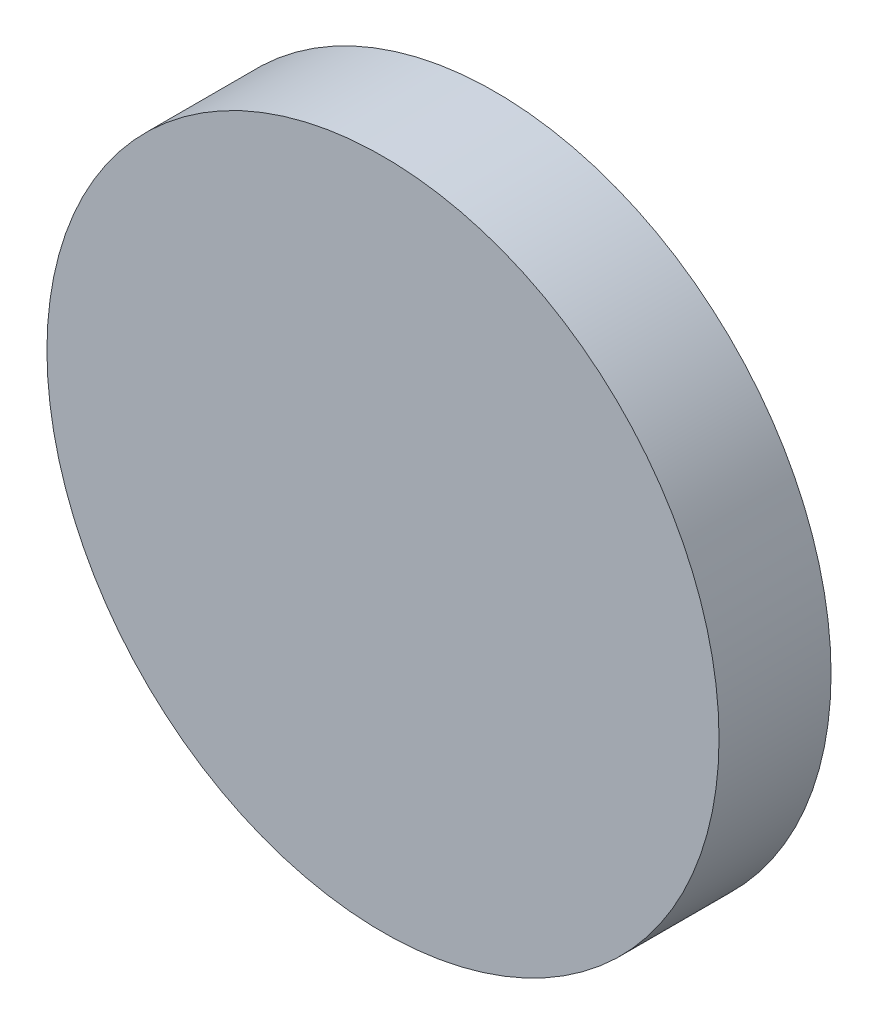
SolidWorks part; units mm, degrees
ref_plane "Front Plane" through (0, 0, 0) normal (0, 0, 1) x (1, 0, 0)
ref_plane "Top Plane" through (0, 0, 0) normal (0, 1, 0) x (1, 0, 0)
ref_plane "Right Plane" through (0, 0, 0) normal (1, 0, 0) x (0, 0, -1)
sketch "Sketch1" plane through (0, 0, 0) normal (0, 0, 1) x (1, 0, 0)
  circle A0 centre (0, 0) radius 6
  dimension "D1" = 12
extrude "Boss-Extrude1" add sketch "Sketch1" along normal blind 2
